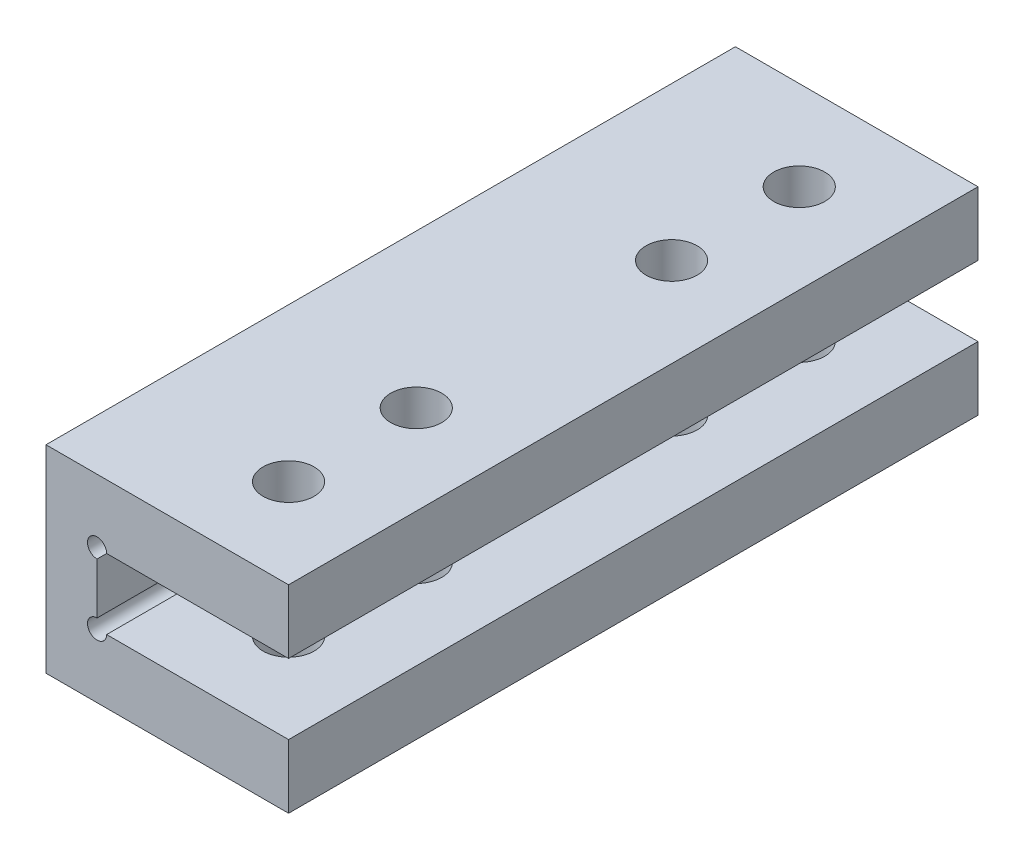
SolidWorks part; units mm, degrees
ref_plane "Front Plane" through (0, 0, 0) normal (0, 0, 1) x (1, 0, 0)
ref_plane "Top Plane" through (0, 0, 0) normal (0, 1, 0) x (1, 0, 0)
ref_plane "Right Plane" through (0, 0, 0) normal (1, 0, 0) x (0, 0, -1)
sketch "Sketch1" plane through (0, 0, 0) normal (0, 1, 0) x (1, 0, 0)
  line L0 (8, 20) -> (8, 10) construction
  line L1 (0, 0) -> (15, 0)
  line L2 (0, 0) -> (0, 27)
  line L3 (0, 27) -> (15, 27)
  line L4 (15, 0) -> (15, 27)
  circle A0 centre (8, 10) radius 2
  circle A1 centre (8, 20) radius 2
  dimension "D4" = 4
  dimension "D6" = 4
  dimension "D7" = 4
  dimension "D1" = 15
  dimension "D2" = 27
  dimension "D3" = 8
  dimension "D5" = 10
  dimension "D8" = 10
extrude "Boss-Extrude1" add sketch "Sketch1" along normal blind 5
sketch "Sketch2" plane through (0, 0, 0) normal (0, 0, 1) x (1, 0, 0)
  line L0 (8.25, 0) -> (-8.25, 0) construction
  line L1 (0, 5) -> (-4, 5)
  line L2 (0, 5) -> (0, -5.5)
  line L3 (0, -5.5) -> (-4, -5.5)
  line L4 (-4, 5) -> (-4, -5.5)
  dimension "D1" = 4
  dimension "D2" = 5.5
extrude "Boss-Extrude2" add sketch "Sketch2" against normal up to surface (27 mm away) up to face at (7.5, 2.5, -27)
ref_plane "Plane1" through (0, -2.75, 0) normal (0, -1, 0) x (-1, 0, 0)
mirror "Mirror3" about plane through (0, -2.75, 0) normal (0, -1, 0) of bodies 102
ref_plane "Plane2" through (0, 0, 0) normal (0, 0, 1) x (1, 0, 0)
mirror "Mirror4" about plane through (0, 5, 0) normal (0, 0, -1) of bodies 105
sketch "Sketch4" plane through (0, 0, 27) normal (0, 0, 1) x (1, 0, 0)
  circle A0 centre (0, 0) radius 0.75
  circle A1 centre (0, -5.5) radius 0.75
  dimension "D1" = 1.5
  dimension "D2" = 1.5
extrude "Cut-Extrude1" cut sketch "Sketch4" against normal up to surface (54 mm away) up to face at (6.5, -2.75, -27)
